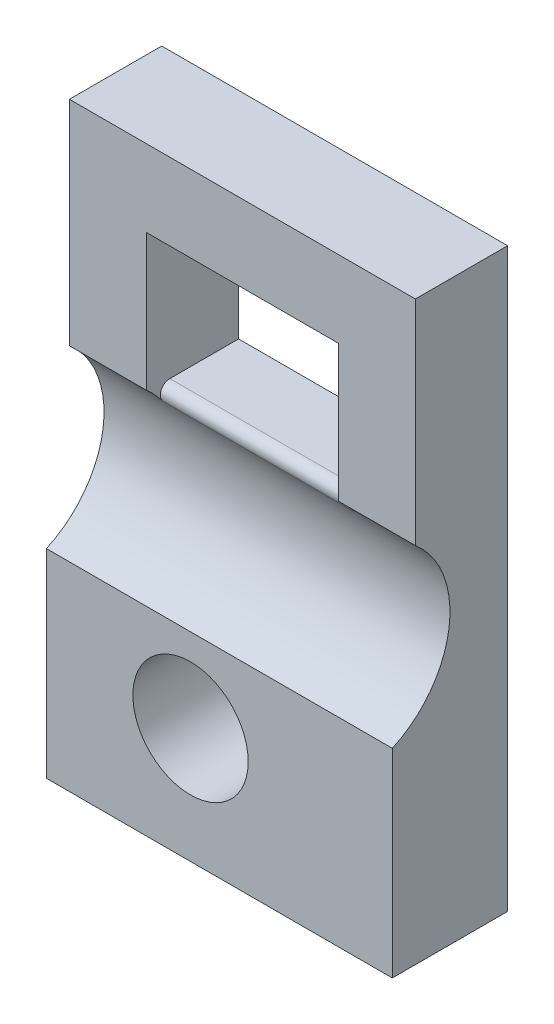
SolidWorks part; units mm, degrees
ref_plane "Front Plane" through (0, 0, 0) normal (0, 0, 1) x (1, 0, 0)
ref_plane "Top Plane" through (0, 0, 0) normal (0, 1, 0) x (1, 0, 0)
ref_plane "Right Plane" through (0, 0, 0) normal (1, 0, 0) x (0, 0, -1)
sketch "Sketch1" plane through (0, 0, 0) normal (0, 0, 1) x (1, 0, 0)
  line L1 (0, 0) -> (18, 0)
  line L2 (0, 0) -> (0, 30)
  line L3 (0, 30) -> (18, 30)
  line L4 (18, 0) -> (18, 30)
  line L5 (4, 26) -> (14, 26)
  line L6 (4, 26) -> (4, 18.8)
  line L7 (4, 18.8) -> (14, 18.8)
  line L8 (14, 26) -> (14, 18.8)
  circle A0 centre (7.5, 6) radius 3
  dimension "D8" = 6
  dimension "D1" = 4
  dimension "D2" = 4
  dimension "D3" = 4
  dimension "D4" = 30
  dimension "D5" = 18
  dimension "D6" = 7.2
  dimension "D7" = 6
  dimension "D9" = 10.5
extrude "Boss-Extrude1" add sketch "Sketch1" along normal blind 6
sketch "Sketch2" plane through (18, 0, 0) normal (1, 0, 0) x (0, 0, -1)
  line L0 (-4.8, 18.8884) -> (-4.8, 30)
  line L1 (-6, 30) -> (0, 30) construction
  line L2 (-4.8, 30) -> (-6, 30)
  line L3 (-6, 30) -> (-6, 10.3524)
  line L4 (-6, 0) -> (-6, 30) construction
  line L5 (-6, 0) -> (0, 0) construction
  line L6 (0, 0) -> (0, 30) construction
  arc A0 (-6, 10.3524) -> (-4.8, 18.8884) centre (-8.1, 15) ccw
  dimension "D1" = 10.2
  dimension "D4" = 3
  dimension "D2" = 15
  dimension "D3" = 4.8
extrude "Cut-Extrude1" cut sketch "Sketch2" against normal through all
fillet "Fillet1" radius 0.5 1 edges at (9, 18.8, 4.6985)
